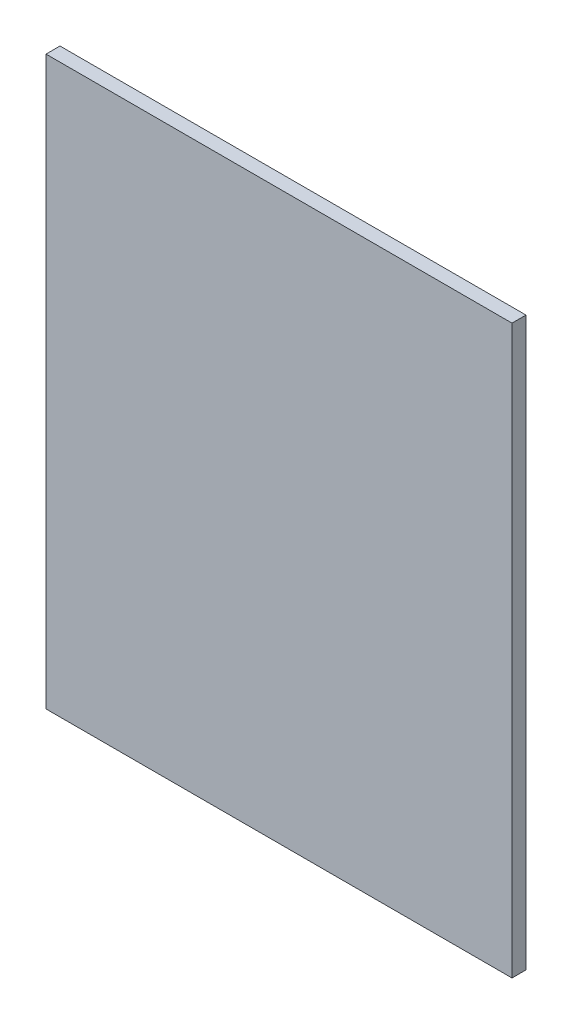
SolidWorks part; units mm, degrees
ref_plane "Front" through (0, 0, 0) normal (0, 0, 1) x (1, 0, 0)
ref_plane "Top" through (0, 0, 0) normal (0, 1, 0) x (1, 0, 0)
ref_plane "Right" through (0, 0, 0) normal (1, 0, 0) x (0, 0, -1)
sketch "Sketch1" plane through (0, 0, 0) normal (0, 0, 1) x (1, 0, 0)
  line L1 (557.5, 678.5) -> (-557.5, 678.5)
  line L2 (557.5, 678.5) -> (557.5, -678.5)
  line L3 (557.5, -678.5) -> (-557.5, -678.5)
  line L4 (-557.5, 678.5) -> (-557.5, -678.5)
  line L5 (557.5, 678.5) -> (-557.5, -678.5) construction
  line L6 (557.5, -678.5) -> (-557.5, 678.5) construction
  point P0 (0, 0)
  dimension "D1" = 1115
  dimension "D2" = 1357
extrude "Boss-Extrude1" add sketch "Sketch1" along normal blind 33.45
